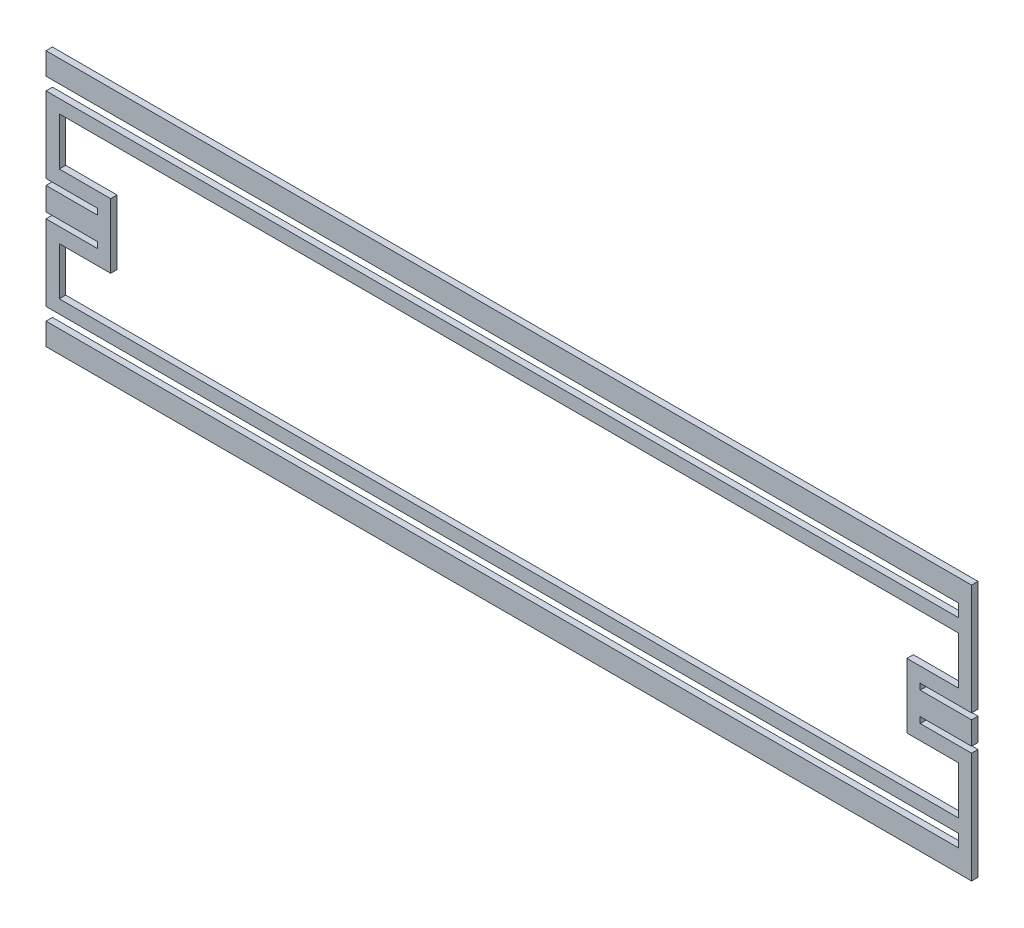
SolidWorks part; units mm, degrees
ref_plane "Front" through (0, 0, 0) normal (0, 0, 1) x (1, 0, 0)
ref_plane "Top" through (0, 0, 0) normal (0, 1, 0) x (1, 0, 0)
ref_plane "Right" through (0, 0, 0) normal (1, 0, 0) x (0, 0, -1)
sketch "Sketch1" plane through (0, 0, 0) normal (0, 0, 1) x (1, 0, 0)
  line L0 (-203.3016, -8.6296) -> (-228.7016, -8.6296)
  line L1 (-228.7016, -8.6296) -> (-228.7016, -46.1359)
  line L2 (-228.7016, -46.1359) -> (222.1484, -46.1359)
  line L3 (222.1484, -46.1359) -> (222.1484, -52.4097)
  line L4 (222.1484, -52.4097) -> (-228.7016, -52.4097)
  line L5 (-228.7016, -52.4097) -> (-228.7016, -63.3285)
  line L6 (-228.7016, -63.3285) -> (228.7016, -63.3285)
  line L7 (228.7016, -63.3285) -> (228.7016, -8.6296)
  line L8 (228.7016, -8.6296) -> (203.3016, -8.6296)
  line L9 (203.3016, -8.6296) -> (203.3016, -5.6579)
  line L10 (203.3016, -5.6579) -> (228.7016, -5.6578)
  line L11 (228.7016, -5.6578) -> (228.7016, 5.6578)
  line L12 (228.7016, 5.6578) -> (203.3016, 5.6579)
  line L13 (203.3016, 5.6579) -> (203.3016, 8.6297)
  line L14 (203.3016, 8.6297) -> (228.7016, 8.6297)
  line L15 (228.7016, 8.6297) -> (228.7016, 63.3285)
  line L16 (228.7016, 63.3285) -> (-228.7016, 63.3285)
  line L17 (-228.7016, 63.3285) -> (-228.7016, 52.4097)
  line L18 (-228.7016, 52.4097) -> (222.1484, 52.4097)
  line L19 (222.1484, 52.4097) -> (222.1484, 46.1359)
  line L20 (222.1484, 46.1359) -> (-228.7016, 46.1359)
  line L21 (-228.7016, 46.1359) -> (-228.7016, 8.6297)
  line L22 (-228.7016, 8.6297) -> (-203.3016, 8.6297)
  line L23 (-203.3016, 8.6297) -> (-203.3016, 5.6579)
  line L24 (-203.3016, 5.6579) -> (-228.7016, 5.6578)
  line L25 (-228.7016, 5.6578) -> (-228.7016, -5.6578)
  line L26 (-228.7016, -5.6578) -> (-203.3016, -5.6579)
  line L27 (-203.3016, -5.6579) -> (-203.3016, -8.6296)
  line L28 (222.1484, -39.5827) -> (222.1484, -15.9766)
  line L29 (222.1484, -15.9766) -> (196.7484, -15.9766)
  line L30 (196.7484, -15.9766) -> (196.7484, 15.9766)
  line L31 (222.1484, 15.9766) -> (222.1484, 39.5827)
  line L32 (196.7484, 15.9766) -> (222.1484, 15.9766)
  line L33 (222.1484, 39.5827) -> (-222.1484, 39.5827)
  line L34 (-222.1484, -39.5827) -> (222.1484, -39.5827)
  line L35 (-222.1484, -15.9766) -> (-222.1484, -39.5827)
  line L36 (-196.7484, -15.9766) -> (-222.1484, -15.9766)
  line L37 (-196.7484, 15.9766) -> (-196.7484, -15.9766)
  line L38 (-222.1484, 15.9766) -> (-196.7484, 15.9766)
  line L39 (-222.1484, 39.5827) -> (-222.1484, 15.9766)
extrude "Boss-Extrude1" add sketch "Sketch1" along normal blind 3.175
